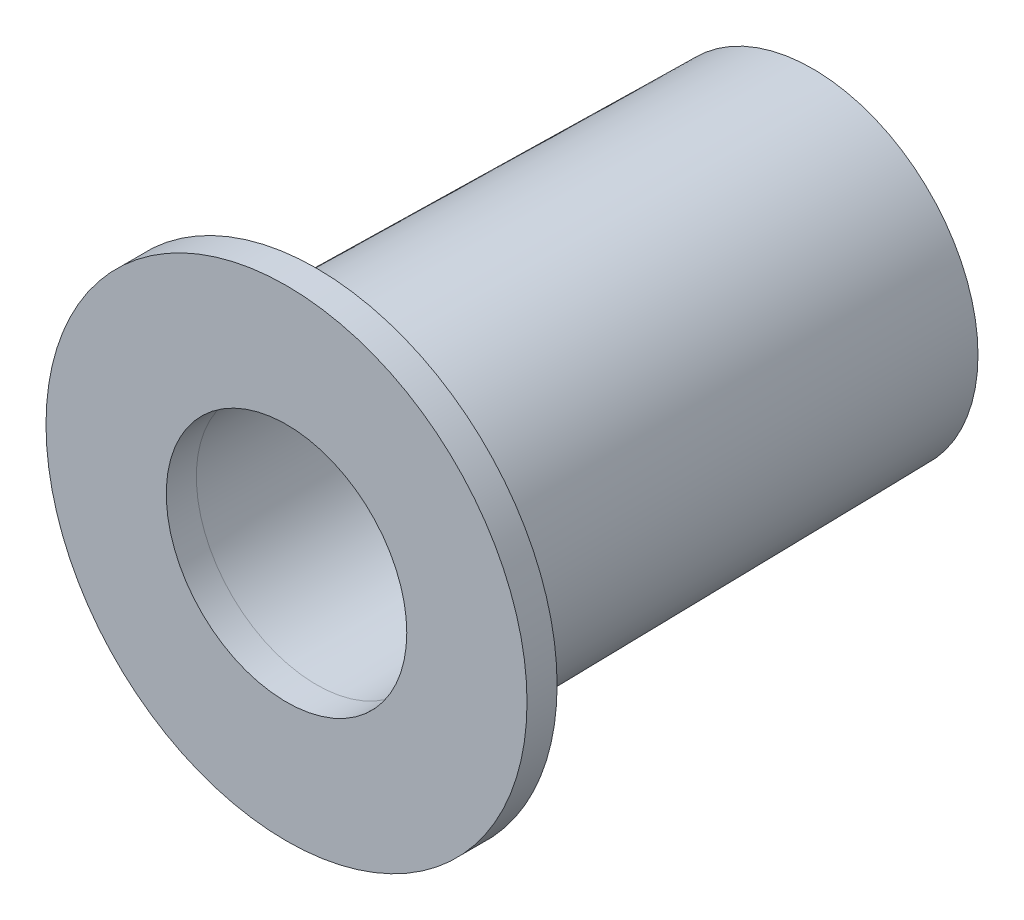
SolidWorks part; units mm, degrees
ref_plane "Front Plane" through (0, 0, 0) normal (0, 0, 1) x (1, 0, 0)
ref_plane "Top Plane" through (0, 0, 0) normal (0, 1, 0) x (1, 0, 0)
ref_plane "Right Plane" through (0, 0, 0) normal (1, 0, 0) x (0, 0, -1)
sketch "Croquis1" plane through (0, 0, 0) normal (0, 0, 1) x (1, 0, 0)
  circle A0 centre (0, 0) radius 11
  dimension "D1" = 22
ref_plane "Plano2" through (0, 0, 33) normal (0, 0, 1) x (1, 0, 0)
sketch "Croquis3" plane through (0, 0, 33) normal (0, 0, 1) x (1, 0, 0)
  circle A0 centre (0, 0) radius 11.5
  dimension "D1" = 23
loft "Recubrir1" add profiles "Croquis1", "Croquis3"
sketch "Croquis4" plane through (0, 0, 0) normal (0, 0, -1) x (-1, 0, 0)
  circle A0 centre (0, 0) radius 7.5
  dimension "D1" = 15
sketch "Croquis5" plane through (0, 0, 33) normal (0, 0, 1) x (1, 0, 0)
  circle A0 centre (0, 0) radius 8
  dimension "D1" = 16
loft "Cortar-Recubrir1" cut profiles "Croquis4", "Croquis5"
sketch "Croquis6" plane through (0, 0, 33) normal (0, 0, 1) x (1, 0, 0)
  circle A0 centre (0, 0) radius 16
  circle A1 centre (0, 0) radius 8 construction
  circle A2 centre (0, 0) radius 8
  dimension "D1" = 32
extrude "Saliente-Extruir1" add sketch "Croquis6" along normal blind 2
